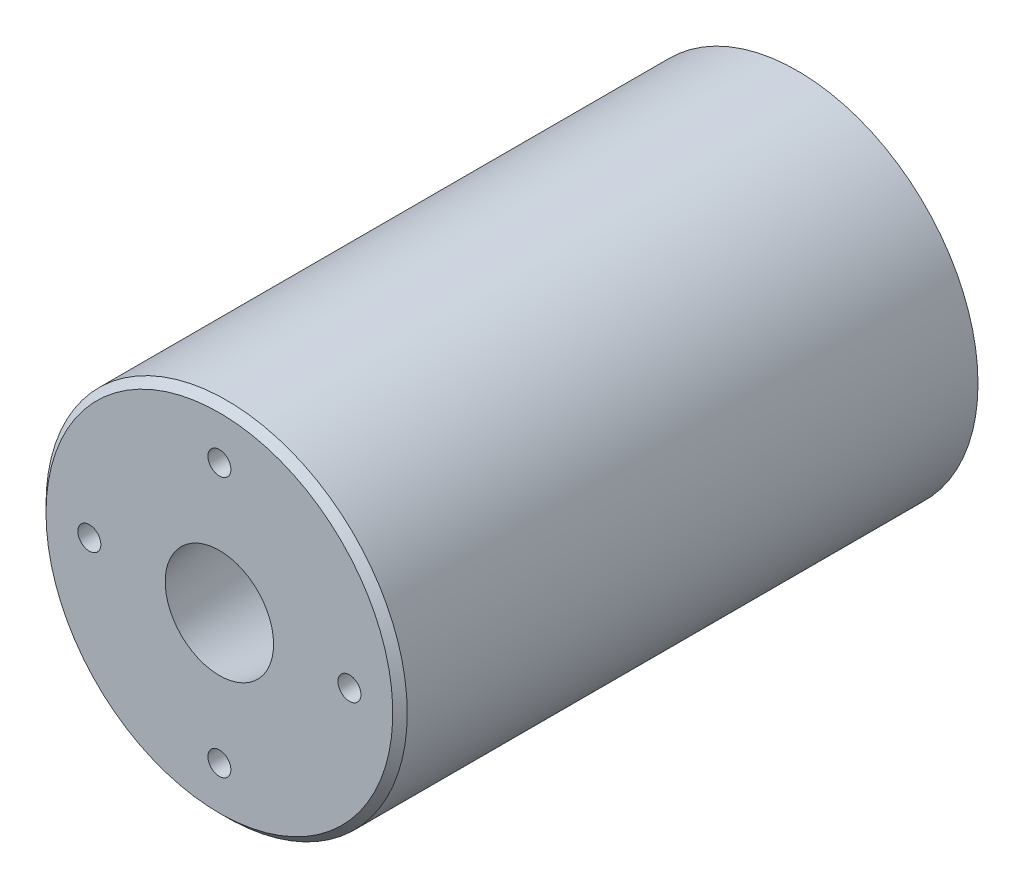
SolidWorks part; units mm, degrees
material "C (Graphite)"
ref_plane "Front Plane" through (0, 0, 0) normal (0, 0, 1) x (1, 0, 0)
ref_plane "Top Plane" through (0, 0, 0) normal (0, 1, 0) x (1, 0, 0)
ref_plane "Right Plane" through (0, 0, 0) normal (1, 0, 0) x (0, 0, -1)
sketch "Sketch1" plane through (0, 0, 0) normal (1, 0, 0) x (0, 0, -1)
  line L0 (-60.9332, 0) -> (57.4263, 0) construction
  line L1 (0, 9.525) -> (101.6, 22.7076)
  line L2 (101.6, 22.7076) -> (101.6, 31.75)
  line L3 (101.6, 31.75) -> (0, 31.75)
  line L4 (0, 31.75) -> (0, 9.525)
  dimension "D1" = 101.6
  dimension "D2" = 9.525
  dimension "D3" = 31.75
  dimension "D4" = 22.7076
revolve "Revolve1" add sketch "Sketch1" angle 360 about L0
hole_wizard "#10-32 Tapped Hole1" positions "Sketch2" profile "Sketch3" tap size "#10-32" standard "ANSI Inch"
sketch "Sketch2" plane through (0, 0, 0) normal (0, 0, 1) x (1, 0, 0)
  point P0 (0, 22.86)
  point P10 (22.86, 0)
  point P11 (0, -22.86)
  point P12 (-22.86, 0)
  point P13 (0, 0)
  dimension "D1" = 22.86
  dimension "D2" = 4
sketch "Sketch3" plane through (0, 22.86, 0) normal (1, 0, 0) x (0, -1, 0)
  line L0 (0, 0) -> (0, 52.0133)
  line L1 (0, 52.0133) -> (2.0193, 50.8)
  line L2 (2.0193, 50.8) -> (2.0193, 0)
  line L5 (2.0193, 0) -> (0, 0)
  line L10 (0, 52.0133) -> (-2.0193, 50.8) construction
  line L11 (0, -6.35) -> (0, 107.95) construction
  dimension "Tap Drill Dia." = 4.0386
  dimension "Tap Drill Depth" = 50.8
  dimension "Drill Angle" = 118
cosmetic thread "Hole Thread1"
cosmetic thread "Hole Thread2"
cosmetic thread "Hole Thread3"
cosmetic thread "Hole Thread4"
chamfer "Chamfer1" distance 1.27 angle 45 1 edges at (31.75, 0, 0)
